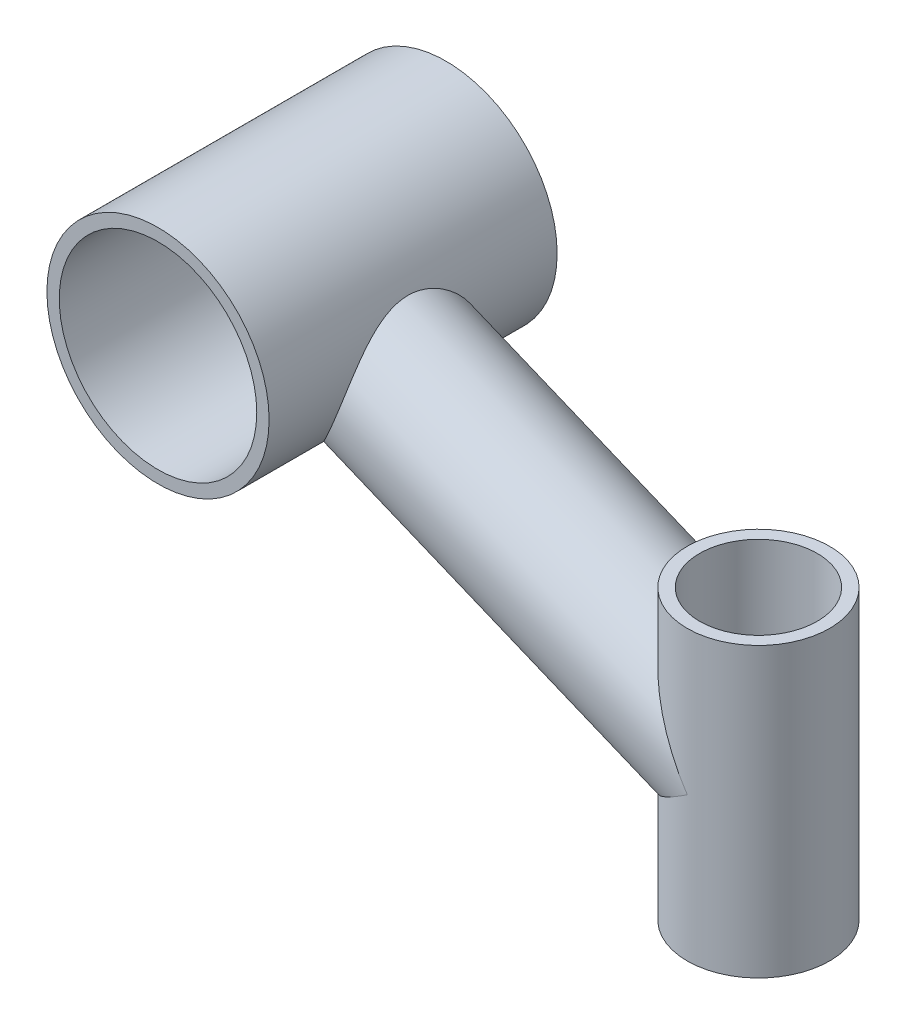
SolidWorks part; units mm, degrees
ref_plane "Plan de face" through (0, 0, 0) normal (0, 0, 1) x (1, 0, 0)
ref_plane "Plan de dessus" through (0, 0, 0) normal (0, 1, 0) x (1, 0, 0)
ref_plane "Plan de droite" through (0, 0, 0) normal (1, 0, 0) x (0, 0, -1)
sketch "Esquisse1" plane through (0, 0, 0) normal (0, 0, 1) x (1, 0, 0)
  circle A0 centre (0, 0) radius 24
  circle A1 centre (0, 0) radius 27
  dimension "D1" = 48
  dimension "D2" = 3
sketch "Esquisse2" plane through (0, 0, 0) normal (1, 0, 0) x (0, 0, -1)
  line L0 (-35, 0) -> (35, 0)
  point P4 (0, 0)
  point P5 (0, 0)
sweep "Balayage1" add profiles "Esquisse1" path "Esquisse2"
sketch "Esquisse3" plane through (0, 0, 0) normal (0, 0, 1) x (1, 0, 0)
  line L0 (0, 0) -> (110.9183, -45.7944)
  dimension "D1" = 120
ref_plane "Plan1" through (0, -45.7944, 0) normal (0, 1, 0) x (1, 0, 0)
sketch "Esquisse5" plane through (0, -45.7944, 0) normal (0, 1, 0) x (1, 0, 0)
  line L0 (0, 0) -> (110.9183, 0) construction
  circle A0 centre (110.9183, 0) radius 14.3
  circle A1 centre (110.9183, 0) radius 17.3
  dimension "D1" = 28.6
  dimension "D2" = 3
ref_plane "Plan2" through (0, 0, 0) normal (0, 0, 1) x (1, 0, 0)
sketch "Esquisse6" plane through (0, 0, 0) normal (0, 0, 1) x (1, 0, 0)
  line L0 (110.9183, -80.7944) -> (110.9183, -10.7944)
  point P3 (110.9183, -45.7944)
  dimension "D1" = 70
sweep "Balayage2" add profiles "Esquisse5" path "Esquisse6"
sketch "Esquisse7" plane through (0, 0, 0) normal (0, 0, 1) x (1, 0, 0)
  line L0 (0, 0) -> (110.9183, -45.7944) construction
  point P0 (55.4591, -22.8972)
ref_plane "Plan3" through (55.4591, -22.8972, 0) normal (0.9243, -0.3816, 0) x (0, 0, -1)
sketch "Esquisse8" plane through (55.4591, -22.8972, 0) normal (0.9243, -0.3816, 0) x (0, 0, -1)
  circle A0 centre (0, 0) radius 17.3
  circle A1 centre (0, 0) radius 14.3
  dimension "D1" = 3
  dimension "D2" = 28.6
extrude "Boss.-Extru.1" add sketch "Esquisse8" along normal up to next and the other way up to next contours A0 | A1
